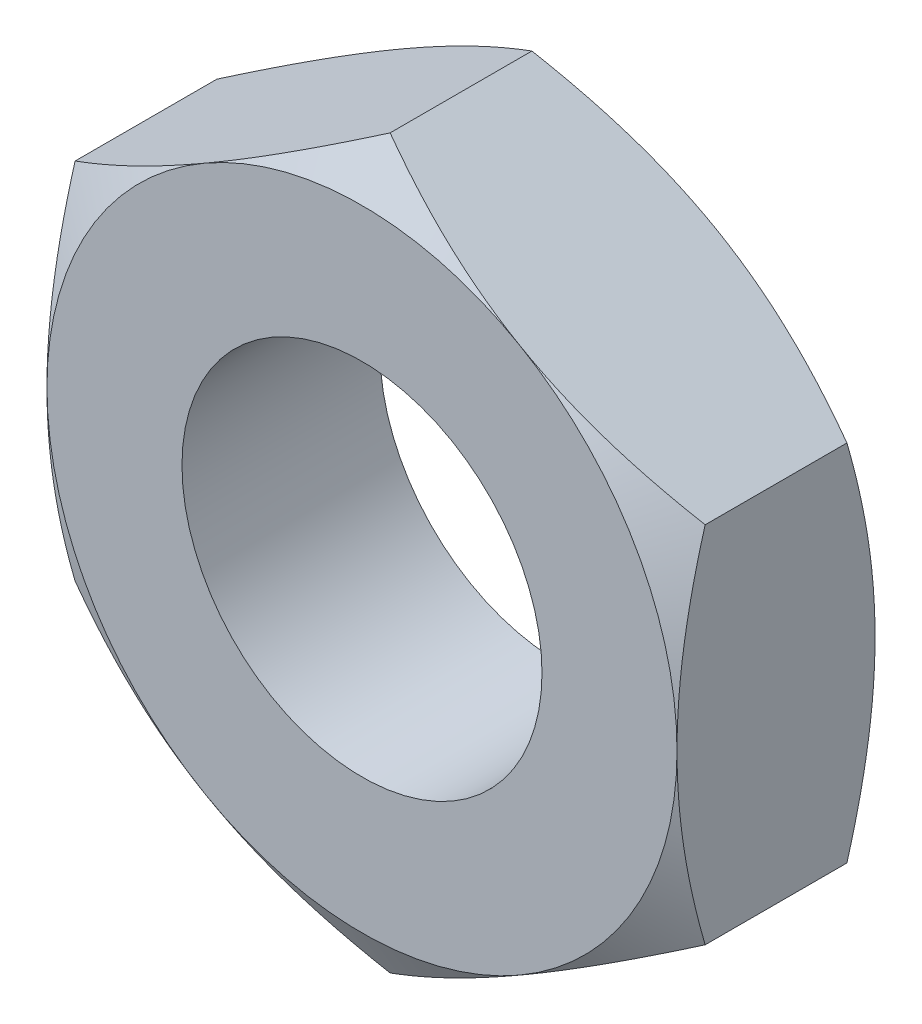
SolidWorks part; units mm, degrees
material "1.4000 (X6Cr13)"
ref_plane "Płaszczyzna XY" through (0, 0, 0) normal (0, 0, 1) x (1, 0, 0)
ref_plane "Płaszczyzna XZ" through (0, 0, 0) normal (0, 1, 0) x (1, 0, 0)
ref_plane "Płaszczyzna YZ" through (0, 0, 0) normal (1, 0, 0) x (0, 0, -1)
sketch "Szkic1" plane through (0, 0, 0) normal (0, 0, 1) x (1, 0, 0)
  line L1 (3.5, 2.0207) -> (0, 4.0415)
  line L2 (0, 4.0415) -> (-3.5, 2.0207)
  line L3 (-3.5, 2.0207) -> (-3.5, -2.0207)
  line L4 (-3.5, -2.0207) -> (0, -4.0415)
  line L5 (0, -4.0415) -> (3.5, -2.0207)
  line L6 (3.5, -2.0207) -> (3.5, 2.0207)
  circle A0 centre (0, 0) radius 3.5 construction
  circle A1 centre (0, 0) radius 2
  dimension "D2" = 4
  dimension "D1" = 7
extrude "Dodanie-wyciągnięcie1" add sketch "Szkic1" along normal blind 2.2
sketch "Szkic2" plane through (0, 0, 0) normal (0, 1, 0) x (1, 0, 0)
  line L0 (-3.5, -2.2) -> (-3.5, 0)
  line L1 (-3.5, -2.2) -> (-3.5, 0) construction
  line L2 (2, 0) -> (2, -2.2)
  line L3 (-3, -2.2) -> (-3, 0)
  line L5 (2, 0) -> (2, -2.2)
  line L6 (-3.5, -2.2) -> (-5.4053, -1.1)
  line L7 (-3.5, -2.2) -> (-3, -2.2)
  line L8 (-5.4053, -1.1) -> (-3.5, 0)
  line L9 (0, -9.8911) -> (0, 0.9366) construction
  line L11 (-3.5, -2.2) -> (-5.4053, -2.2)
  line L13 (-3.5, 0) -> (-5.4053, 0)
  line L14 (-5.4053, -2.2) -> (-5.4053, 0)
  dimension "D1" = 30
  dimension "D2" = 60
revolve "Wycięcie-obrót1" cut sketch "Szkic2" angle 360 about L9
